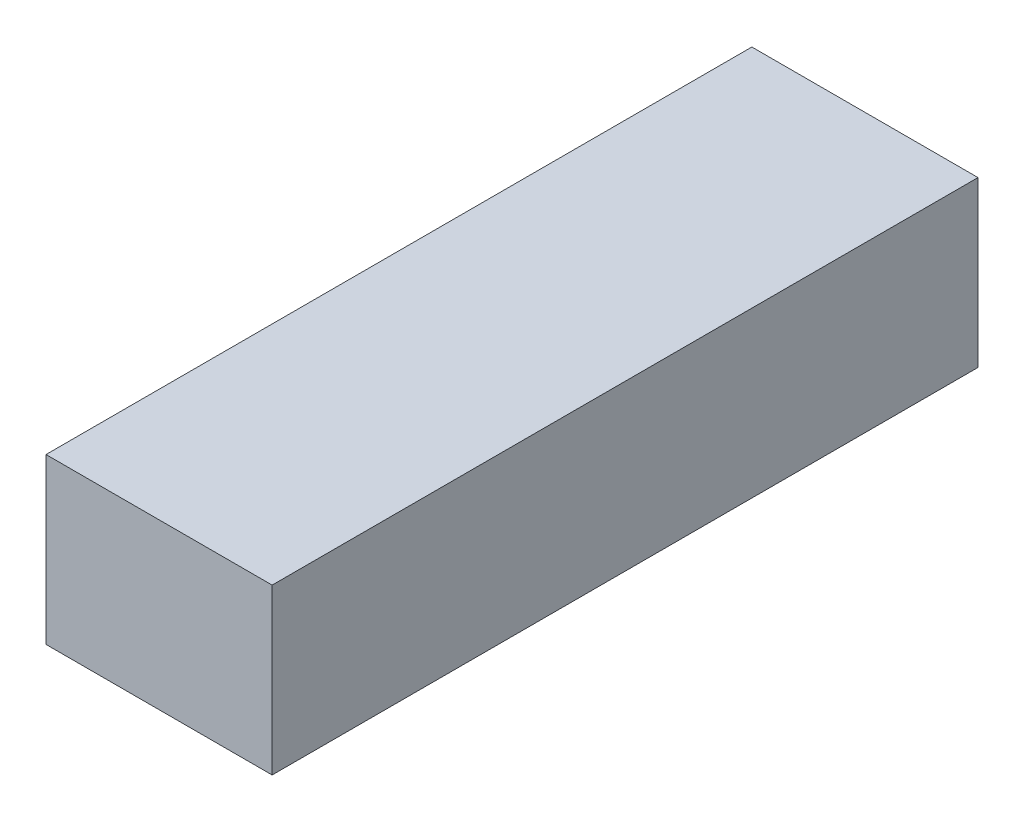
SolidWorks part; units mm, degrees
ref_plane "Front Plane" through (0, 0, 0) normal (0, 0, 1) x (1, 0, 0)
ref_plane "Top Plane" through (0, 0, 0) normal (0, 1, 0) x (1, 0, 0)
ref_plane "Right Plane" through (0, 0, 0) normal (1, 0, 0) x (0, 0, -1)
sketch "Sketch1" plane through (0, 0, 0) normal (0, 1, 0) x (1, 0, 0)
  line L1 (-16.5, -51.5) -> (16.5, -51.5)
  line L2 (-16.5, -51.5) -> (-16.5, 51.5)
  line L3 (-16.5, 51.5) -> (16.5, 51.5)
  line L4 (16.5, -51.5) -> (16.5, 51.5)
  line L5 (-16.5, -51.5) -> (16.5, 51.5) construction
  line L6 (-16.5, 51.5) -> (16.5, -51.5) construction
  point P0 (0, 0)
  dimension "D1" = 103
  dimension "D2" = 33
extrude "Boss-Extrude1" add sketch "Sketch1" along normal blind 24
ref_plane "Plane1" through (0, 0, 0) normal (-1, 0, 0) x (0, 0, 1)
